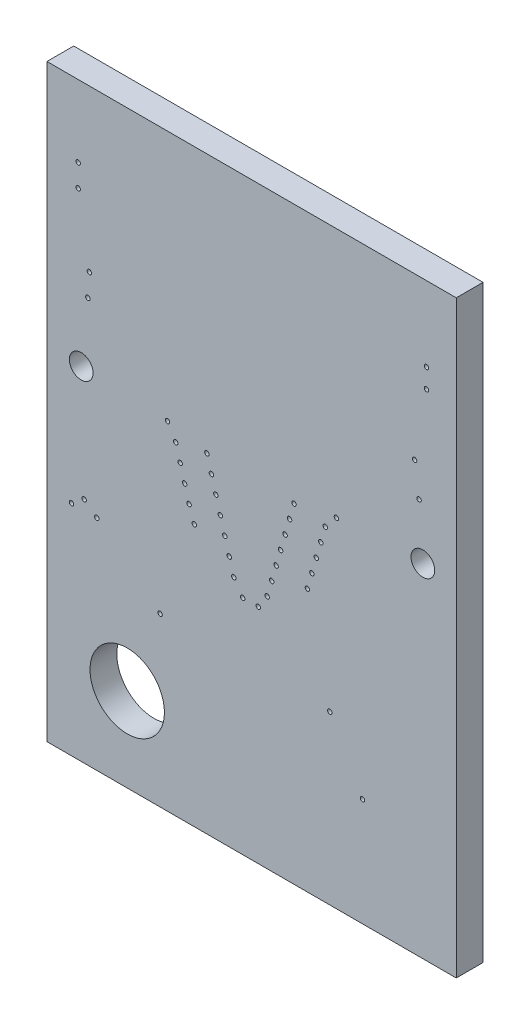
SolidWorks part; units mm, degrees
ref_plane "Front Plane" through (0, 0, 0) normal (0, 0, 1) x (1, 0, 0)
ref_plane "Top Plane" through (0, 0, 0) normal (0, 1, 0) x (1, 0, 0)
ref_plane "Right Plane" through (0, 0, 0) normal (1, 0, 0) x (0, 0, -1)
ref_plane "Dielectric_Layer Layer 1" through (0, 0, 1.6) normal (0, 0, 1) x (1, 0, 0)
sketch "Sketch1" plane through (0, 0, 0) normal (0, 0, 1) x (1, 0, 0)
  line L0 (0, 0) -> (0, 20.1041)
  line L1 (0, 20.1041) -> (13.97, 20.1041)
  line L2 (13.97, 20.1041) -> (13.97, 0)
  line L3 (13.97, 0) -> (0, 0)
extrude "Board_Outline" add sketch "Sketch1" along normal blind 0.9144 separate body
sketch "Sketch2" plane through (0, 0, 0) normal (0, 0, 1) x (1, 0, 0)
  circle A0 centre (10.7696, 3.683) radius 0.0762
  circle A1 centre (12.954, 16.891) radius 0.0762
  circle A2 centre (1.0668, 17.653) radius 0.0762
  circle A3 centre (1.4478, 14.605) radius 0.0762
  circle A4 centre (1.397, 13.8176) radius 0.0762
  circle A5 centre (4.1148, 11.5316) radius 0.0762
  circle A6 centre (4.3942, 11.049) radius 0.0762
  circle A7 centre (4.5466, 10.5156) radius 0.0762
  circle A8 centre (4.699, 9.9822) radius 0.0762
  circle A9 centre (4.8514, 9.4488) radius 0.0762
  circle A10 centre (5.0292, 8.9408) radius 0.0762
  circle A11 centre (5.461, 11.2522) radius 0.0762
  circle A12 centre (5.6134, 10.7188) radius 0.0762
  circle A13 centre (5.7658, 10.1854) radius 0.0762
  circle A14 centre (5.9182, 9.652) radius 0.0762
  circle A15 centre (6.0706, 9.1186) radius 0.0762
  circle A16 centre (6.223, 8.5852) radius 0.0762
  circle A17 centre (6.3754, 8.0518) radius 0.0762
  circle A18 centre (6.6802, 7.5946) radius 0.0762
  circle A19 centre (12.5476, 14.605) radius 0.0762
  circle A20 centre (12.7, 13.5128) radius 0.0762
  circle A21 centre (9.8806, 11.557) radius 0.0762
  circle A22 centre (9.4996, 11.0998) radius 0.0762
  circle A23 centre (9.3472, 10.5664) radius 0.0762
  circle A24 centre (9.1948, 10.033) radius 0.0762
  circle A25 centre (9.0424, 9.4996) radius 0.0762
  circle A26 centre (8.89, 8.9662) radius 0.0762
  circle A27 centre (8.4328, 11.2522) radius 0.0762
  circle A28 centre (8.2804, 10.7188) radius 0.0762
  circle A29 centre (8.128, 10.1854) radius 0.0762
  circle A30 centre (7.9756, 9.652) radius 0.0762
  circle A31 centre (7.8232, 9.1186) radius 0.0762
  circle A32 centre (7.6708, 8.5852) radius 0.0762
  circle A33 centre (7.5184, 8.0518) radius 0.0762
  circle A34 centre (7.2136, 7.5946) radius 0.0762
  circle A35 centre (1.7018, 7.4676) radius 0.0762
  circle A36 centre (1.27, 7.7978) radius 0.0762
  circle A37 centre (0.8382, 7.4676) radius 0.0762
  circle A38 centre (12.954, 17.5514) radius 0.0762
  circle A39 centre (1.0668, 16.891) radius 0.0762
  circle A40 centre (9.652, 5.715) radius 0.0762
  circle A41 centre (3.8608, 5.715) radius 0.0762
extrude "NPTH" cut sketch "Sketch2" along normal through all
sketch "Sketch3" plane through (0, 0, 0) normal (0, 0, 1) x (1, 0, 0)
  circle A0 centre (12.83, 11.68) radius 0.405
  circle A1 centre (2.74, 2.87) radius 1.27
  circle A2 centre (1.17, 11.68) radius 0.405
extrude "PTH" cut sketch "Sketch3" along normal through all
